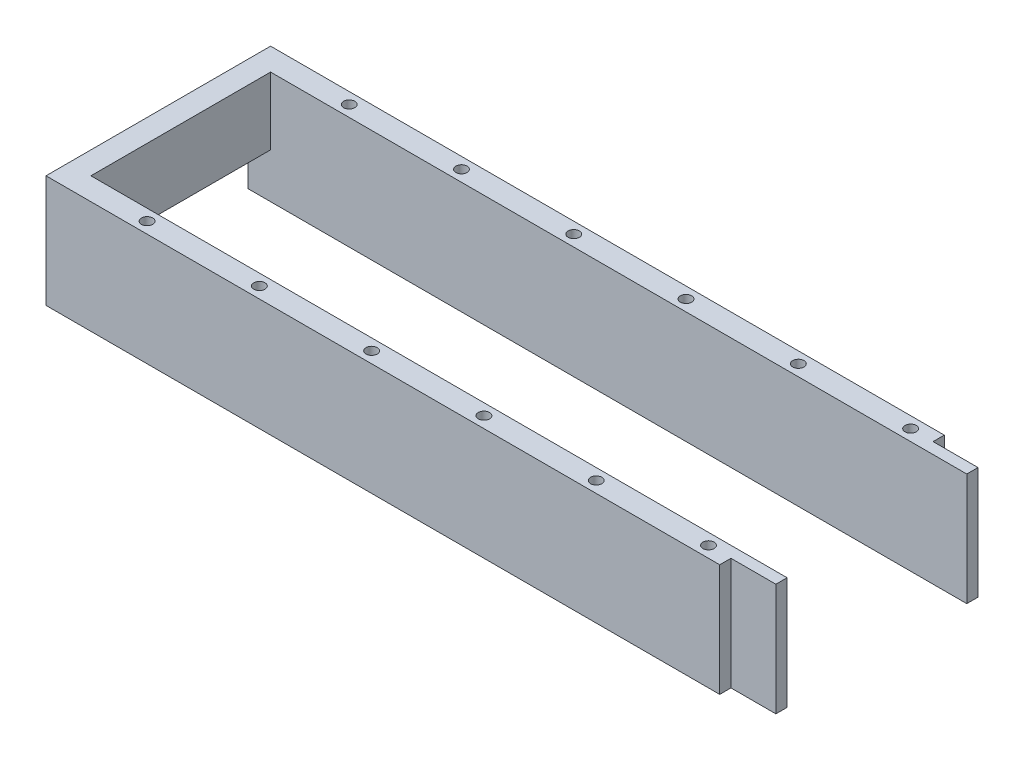
SolidWorks part; units mm, degrees
ref_plane "Front Plane" through (0, 0, 0) normal (0, 0, 1) x (1, 0, 0)
ref_plane "Top Plane" through (0, 0, 0) normal (0, 1, 0) x (1, 0, 0)
ref_plane "Right Plane" through (0, 0, 0) normal (1, 0, 0) x (0, 0, -1)
sketch "Sketch2" plane through (0, 0, 0) normal (0, 1, 0) x (1, 0, 0)
  line L0 (-101.6, 0) -> (101.6, 0) construction
  line L1 (-101.6, -3.175) -> (101.6, -3.175)
  line L2 (-101.6, -3.175) -> (-101.6, 3.175)
  line L3 (-101.6, 3.175) -> (101.6, 3.175)
  line L4 (101.6, -3.175) -> (101.6, 3.175)
  line L5 (-101.6, -3.175) -> (101.6, 3.175) construction
  line L6 (-101.6, 3.175) -> (101.6, -3.175) construction
  circle A0 centre (-76.2, 0) radius 1.5875
  circle A1 centre (-44.45, 0) radius 1.5875
  circle A2 centre (-12.7, 0) radius 1.5875
  circle A3 centre (19.05, 0) radius 1.5875
  circle A4 centre (50.8, 0) radius 1.5875
  circle A5 centre (82.55, 0) radius 1.5875
  circle A7 centre (114.3, 0) radius 1.5875 [skipped]
  point P0 (0, 0)
  dimension "D3" = 3.175
  dimension "D1" = 6.35
  dimension "D2" = 203.2
  dimension "D4" = 25.4
  dimension "D6" = 31.75
  dimension "D5" = 7
extrude "Boss-Extrude1" add sketch "Sketch2" along normal blind 31.75
sketch "Sketch4" plane through (0, 0, 3.175) normal (0, 0, 1) x (1, 0, 0)
  line L0 (-101.6, 0) -> (101.6, 0) construction
  line L1 (-101.6, 31.75) -> (-95.25, 31.75)
  line L2 (-101.6, 31.75) -> (-101.6, 12.7)
  line L3 (-101.6, 12.7) -> (-95.25, 12.7)
  line L4 (-95.25, 31.75) -> (-95.25, 12.7)
  dimension "D1" = 6.35
  dimension "D2" = 12.7
extrude "Boss-Extrude2" add sketch "Sketch4" along normal blind 50.8
ref_plane "Plane1" through (0, 0, 28.575) normal (0, 0, 1) x (1, 0, 0)
mirror "Mirror1" about plane through (0, 0, 28.575) normal (0, 0, 1) of "Boss-Extrude1"
sketch "Sketch6" plane through (0, 31.75, 0) normal (0, 1, 0) x (1, 0, 0)
  line L16 (101.6, 3.175) -> (88.9, 3.175)
  line L17 (101.6, 3.175) -> (101.6, 0)
  line L18 (101.6, 0) -> (88.9, 0)
  line L19 (88.9, 3.175) -> (88.9, 0)
  line L20 (101.6, -60.325) -> (88.9, -60.325)
  line L21 (101.6, -60.325) -> (101.6, -57.15)
  line L22 (101.6, -57.15) -> (88.9, -57.15)
  line L23 (88.9, -60.325) -> (88.9, -57.15)
  dimension "D1" = 3.175
  dimension "D2" = 12.7
  dimension "D3" = 3.175
  dimension "D4" = 12.7
extrude "Cut-Extrude1" cut sketch "Sketch6" against normal through all
